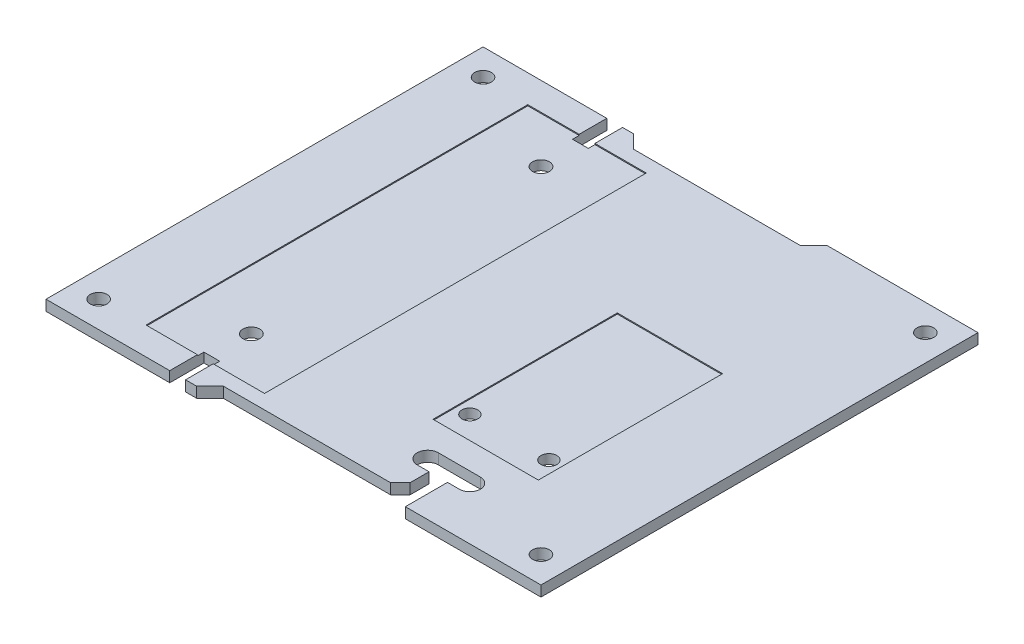
SolidWorks part; units mm, degrees
ref_plane "Front Plane" through (0, 0, 0) normal (0, 0, 1) x (1, 0, 0)
ref_plane "Top Plane" through (0, 0, 0) normal (0, 1, 0) x (1, 0, 0)
ref_plane "Right Plane" through (0, 0, 0) normal (1, 0, 0) x (0, 0, -1)
sketch "Sketch1" plane through (0, 0, 0) normal (0, 1, 0) x (1, 0, 0)
  line L1 (-47, -41.5) -> (47, -41.5)
  line L2 (-47, -41.5) -> (-47, 41.5)
  line L3 (-47, 41.5) -> (47, 41.5)
  line L4 (47, -41.5) -> (47, 41.5)
  line L5 (-47, -41.5) -> (47, 41.5) construction
  line L6 (-47, 41.5) -> (47, -41.5) construction
  line L7 (-42, -36.5) -> (42, -36.5) construction
  line L8 (-42, -36.5) -> (-42, 36.5) construction
  line L9 (-42, 36.5) -> (42, 36.5) construction
  line L10 (42, -36.5) -> (42, 36.5) construction
  line L11 (-42, -36.5) -> (42, 36.5) construction
  line L12 (-42, 36.5) -> (42, -36.5) construction
  circle A0 centre (-42, 36.5) radius 1.5875
  circle A1 centre (42, 36.5) radius 1.5875
  circle A2 centre (42, -36.5) radius 1.5875
  circle A3 centre (-42, -36.5) radius 1.5875
  point P0 (0, 0)
  point P14 (0, 0)
  dimension "D3" = 3.175
  dimension "D1" = 83
  dimension "D2" = 94
  dimension "D4" = 5
  dimension "D5" = 5
extrude "Boss-Extrude1" add sketch "Sketch1" along normal blind 2
sketch "Sketch2" plane through (0, 2, 0) normal (0, 1, 0) x (1, 0, 0)
  line L0 (0, 41.5) -> (0, -41.5) construction
  line L1 (47, 41.5) -> (-47, 41.5) construction
  line L2 (-47, -41.5) -> (47, -41.5) construction
  line L3 (-47, 0) -> (47, 0) construction
  line L4 (-47, 41.5) -> (-47, -41.5) construction
  line L5 (47, -41.5) -> (47, 41.5) construction
  line L6 (-22, 36) -> (-22, -36) construction
  line L7 (-33, 36) -> (-11, 36) construction
  line L8 (-33, 36) -> (-33, -36) construction
  line L9 (-33, -36) -> (-11, -36) construction
  line L10 (-11, 36) -> (-11, -36) construction
  line L11 (-33, 36) -> (-11, -36) construction
  line L12 (-33, -36) -> (-11, 36) construction
  line L13 (12, -20) -> (27, -20) construction
  line L14 (-23.5, 41.5) -> (-20.5, 41.5)
  line L15 (-23.5, 41.5) -> (-23.5, 35)
  line L16 (-23.5, 35) -> (-20.5, 35)
  line L17 (-20.5, 41.5) -> (-20.5, 35)
  line L18 (-23.5, 41.5) -> (-20.5, 35) construction
  line L19 (-23.5, 35) -> (-20.5, 41.5) construction
  line L20 (-23.5, -41.5) -> (-20.5, -41.5)
  line L21 (-23.5, -41.5) -> (-23.5, -35)
  line L22 (-23.5, -35) -> (-20.5, -35)
  line L23 (-20.5, -41.5) -> (-20.5, -35)
  line L24 (-23.5, -41.5) -> (-20.5, -35) construction
  line L25 (-23.5, -35) -> (-20.5, -41.5) construction
  line L26 (15.5, -31.5) -> (23.5, -31.5) construction
  line L27 (15.5, -29.5) -> (23.5, -29.5)
  line L28 (15.5, -33.5) -> (17.75, -33.5)
  line L29 (21.25, -33.5) -> (23.5, -33.5)
  line L31 (17.75, -33.5) -> (17.75, -41.5)
  line L32 (17.75, -41.5) -> (21.25, -41.5)
  line L33 (21.25, -33.5) -> (21.25, -41.5)
  line L34 (17.75, -33.5) -> (21.25, -41.5) construction
  line L35 (17.75, -41.5) -> (21.25, -33.5) construction
  line L36 (13.5, -20) -> (13.5, -35) construction
  line L37 (25.5, -20) -> (25.5, -37.6307) construction
  circle A2 centre (-22, -27.5) radius 1.6
  circle A3 centre (-22, 27.5) radius 1.6
  circle A4 centre (12, -20) radius 1.5
  circle A5 centre (27, -20) radius 1.5
  arc A6 (15.5, -29.5) -> (15.5, -33.5) centre (15.5, -31.5) ccw
  arc A7 (23.5, -33.5) -> (23.5, -29.5) centre (23.5, -31.5) ccw
  point P16 (-22, 0)
  point P27 (-22, 38.25)
  point P32 (-22, -38.25)
  point P37 (19.5, -20)
  point P40 (19.9612, -31.2528)
  point P49 (19.5, -37.5)
  dimension "D4" = 3.2
  dimension "D10" = 3
  dimension "D1" = 72
  dimension "D2" = 22
  dimension "D3" = 25
  dimension "D5" = 55
  dimension "D6" = 27.5
  dimension "D7" = 2
  dimension "D8" = 3
  dimension "D9" = 1.5
  dimension "D11" = 15
  dimension "D12" = 20
  dimension "D13" = 20
  dimension "D14" = 3.5
  dimension "D15" = 10
  dimension "D16" = 4
extrude "Cut-Extrude1" cut sketch "Sketch2" against normal through all
sketch "Sketch3" plane through (0, 2, 0) normal (0, 1, 0) x (1, 0, 0)
  line L0 (0, 0) -> (-47, 0) construction
  line L1 (-33.25, 36.25) -> (-10.75, 36.25)
  line L2 (-33.25, 36.25) -> (-33.25, -36.25)
  line L3 (-33.25, -36.25) -> (-10.75, -36.25)
  line L4 (-10.75, 36.25) -> (-10.75, -36.25)
  line L5 (-33.25, 36.25) -> (-10.75, -36.25) construction
  line L6 (-33.25, -36.25) -> (-10.75, 36.25) construction
  line L7 (-47, 41.5) -> (-47, -41.5) construction
  line L8 (-22, -27.5) -> (-22, 27.5) construction
  line L10 (9.5, -24.5) -> (29.5, -24.5)
  line L11 (9.5, -24.5) -> (9.5, 10.5)
  line L12 (9.5, 10.5) -> (29.5, 10.5)
  line L13 (29.5, -24.5) -> (29.5, 10.5)
  line L14 (9.5, -24.5) -> (29.5, 10.5) construction
  line L15 (9.5, 10.5) -> (29.5, -24.5) construction
  circle A0 centre (12, -20) radius 1.5 construction
  point P4 (-22, 0)
  point P18 (19.5, -7)
  dimension "D1" = 72.5
  dimension "D2" = 22.5
  dimension "D3" = 35
  dimension "D4" = 20
  dimension "D5" = 2.5
  dimension "D6" = 4.5
extrude "Cut-Extrude2" cut sketch "Sketch3" against normal blind 0.2
sketch "Sketch4" plane through (0, 2, 0) normal (0, 1, 0) x (1, 0, 0)
  line L0 (-18.415, -41.5) -> (-15.875, -38.96)
  line L1 (-20.5, -41.5) -> (17.75, -41.5) construction
  line L2 (-15.875, -38.96) -> (15.875, -38.96)
  line L5 (0, 0) -> (0, -38.96) construction
  line L6 (17.75, -33.5) -> (17.75, -41.5) construction
  line L8 (17.75, -41.5) -> (-18.415, -41.5)
  line L9 (15.875, -38.96) -> (17.75, -37.085)
  line L10 (17.75, -37.085) -> (17.75, -41.5)
  line L11 (-18.415, 41.5) -> (-15.875, 38.96)
  line L12 (47, 41.5) -> (-20.5, 41.5) construction
  line L13 (-15.875, 38.96) -> (15.875, 38.96)
  line L14 (15.875, 38.96) -> (18.415, 41.5)
  line L15 (0, 0) -> (0, 38.96) construction
  point P4 (0, -38.96)
  point P19 (0, 0)
  line M15 (-20.5, -41.5) -> (17.75, -41.5)
  line M16 (17.75, -41.5) -> (17.75, -33.5)
  line M25 (47, 41.5) -> (-20.5, 41.5)
  dimension "D1" = 31.75
  dimension "D3" = 45
  dimension "D4" = 2.54
  dimension "D2" = 45
  dimension "D5" = 2.54
  dimension "D6" = 45
  dimension "D7" = 45
  dimension "D8" = 31.75
extrude "Cut-Extrude3" cut sketch "Sketch4" against normal through all contours L13 L14 L11 M25 | L9 L2 L0 M15 M16
equation "\"D5@Sketch1\"=\"D4@Sketch1\""
equation "\"D6@Sketch2\"=\"D5@Sketch2\"/2"
equation "\"D9@Sketch2\"=\"D8@Sketch2\"/2"
equation "\"D7@Sketch4\"=\"D6@Sketch4\""
